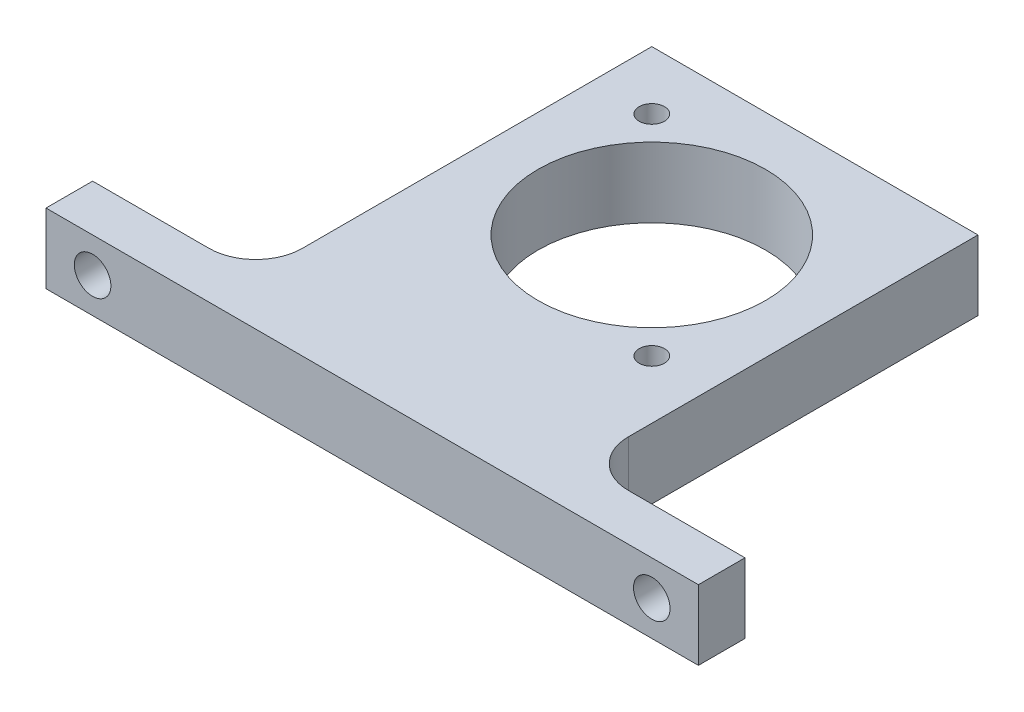
SolidWorks part; units mm, degrees
material "6061-T6 (SS)"
ref_plane "Front Plane" through (0, 0, 0) normal (0, 0, 1) x (1, 0, 0)
ref_plane "Top Plane" through (0, 0, 0) normal (0, 1, 0) x (1, 0, 0)
ref_plane "Right Plane" through (0, 0, 0) normal (1, 0, 0) x (0, 0, -1)
sketch "Sketch1" plane through (0, 0, 0) normal (0, 1, 0) x (1, 0, 0)
  line L1 (-22.225, 22.225) -> (22.225, 22.225)
  line L2 (-22.225, 22.225) -> (-22.225, -38.1)
  line L3 (-22.225, -38.1) -> (22.225, -38.1)
  line L4 (22.225, 22.225) -> (22.225, -38.1)
  circle A0 centre (0, 0) radius 11.1125 construction
  point P7 (0, 22.225)
  dimension "D1" = 22.225
  dimension "D2" = 38.1
  dimension "D3" = 22.225
  dimension "D4" = 22.225
extrude "Boss-Extrude1" add sketch "Sketch1" along normal blind 9.525
sketch "Sketch2" plane through (0, 0, 0) normal (0, -1, 0) x (1, 0, 0)
  line L0 (-22.225, -22.225) -> (-22.225, 38.1) construction
  line L1 (-22.225, 38.1) -> (22.225, 38.1) construction
  line L2 (22.225, 38.1) -> (22.225, -22.225) construction
  line L3 (22.225, -22.225) -> (-22.225, -22.225) construction
  line L4 (-22.225, -22.225) -> (-22.225, 38.1)
  line L5 (-22.225, 38.1) -> (22.225, 38.1)
  line L6 (22.225, 38.1) -> (22.225, -22.225)
  line L7 (22.225, -22.225) -> (-22.225, -22.225)
sketch "Sketch6" plane through (0, 9.525, 0) normal (0, 1, 0) x (1, 0, 0)
  line L9 (-22.225, 22.225) -> (-22.225, -38.1)
  line L10 (-22.225, -38.1) -> (22.225, -38.1)
  line L11 (22.225, -38.1) -> (22.225, 22.225)
  line L12 (22.225, 22.225) -> (-22.225, 22.225)
  line L13 (-22.225, 22.225) -> (-22.225, -38.1) construction
  line L14 (-22.225, -38.1) -> (22.225, -38.1) construction
  line L15 (22.225, -38.1) -> (22.225, 22.225) construction
  line L16 (22.225, 22.225) -> (-22.225, 22.225) construction
  dimension "D1" = 0
sketch "Sketch7" plane through (0, 0, 38.1) normal (0, 0, 1) x (1, 0, 0)
  line L0 (-22.225, 9.525) -> (-44.45, 9.525)
  line L1 (-44.45, 9.525) -> (-44.45, 0)
  line L2 (-44.45, 0) -> (44.45, 0)
  line L3 (44.45, 0) -> (44.45, 9.525)
  line L4 (-22.225, 9.525) -> (-22.225, 0)
  line L5 (-22.225, 0) -> (22.225, 0)
  line L6 (22.225, 0) -> (22.225, 9.525)
  line L7 (22.225, 9.525) -> (-22.225, 9.525)
  line L8 (-22.225, 9.525) -> (-22.225, 0) construction
  line L10 (22.225, 0) -> (22.225, 9.525) construction
  line L11 (22.225, 9.525) -> (-22.225, 9.525) construction
  line L12 (44.45, 9.525) -> (-44.45, 9.525)
  line L17 (-22.225, 0) -> (22.225, 0)
  point P8 (0, 0)
  point P9 (0, 9.525)
  dimension "D2" = 88.9
  dimension "D1" = 0
extrude "Boss-Extrude3" add sketch "Sketch7" against normal blind 6.35
fillet "Fillet1" radius 6.35 2 edges at (22.225, 4.7625, 31.75) (-22.225, 4.7625, 31.75)
sketch "Sketch8" plane through (0, 0, 38.1) normal (0, 0, 1) x (1, 0, 0)
  line L1 (44.45, 0) -> (44.45, 9.525) construction
  line L2 (0, 0) -> (0, 30.8683) construction
  circle A0 centre (-38.1, 4.7625) radius 2.4892
  circle A1 centre (38.1, 4.7625) radius 2.4892
  point P9 (44.45, 4.7625)
  dimension "D1" = 4.9784
  dimension "D2" = 38.1
extrude "Cut-Extrude1" cut sketch "Sketch8" against normal up to surface (6.35 mm away)
sketch "Sketch9" plane through (0, 0, 38.1) normal (0, 0, 1) x (1, 0, 0)
  line L0 (0, 0) -> (0, 29.1158) construction
  circle A2 centre (-38.1, 1.9844) radius 3.4925
  circle A3 centre (38.1, 1.9844) radius 3.4925
  dimension "D1" = 6.985
  dimension "D2" = 38.1
sketch "Sketch10" plane through (0, 9.525, 0) normal (0, 1, 0) x (1, 0, 0)
  line L0 (29.8509, -29.8509) -> (-29.8509, 29.8509) construction
  line L1 (0, 0) -> (0, 68.8246) construction
  circle A0 centre (0, 0) radius 15.494
  circle A1 centre (0, 0) radius 20.193 construction
  circle A2 centre (-14.2786, 14.2786) radius 1.7272
  circle A3 centre (14.2786, -14.2786) radius 1.7272
  point P6 (0, 0)
  dimension "D1" = 30.988
  dimension "D2" = 3.4544
  dimension "D3" = 40.386
  dimension "D4" = 45
extrude "Cut-Extrude2" cut sketch "Sketch10" against normal up to next
hole_wizard "#8-32 Tapped Hole2" positions "Sketch13" profile "Sketch14" tap size "#8-32" standard "ANSI Inch" end condition through all
sketch "Sketch13" plane through (0, 9.525, 0) normal (0, 1, 0) x (1, 0, 0)
  point P0 (-14.2786, 14.2786)
  point P3 (14.2786, -14.2786)
sketch "Sketch14" plane through (-14.2786, 9.525, -14.2786) normal (1, 0, 0) x (0, 0, 1)
  line L0 (0, 0) -> (0, 9.525)
  line L1 (0, 9.525) -> (1.7272, 9.525)
  line L2 (1.7272, 9.525) -> (1.7272, 0)
  line L5 (1.7272, 0) -> (0, 0)
  line L11 (0, -6.35) -> (0, 107.95) construction
  dimension "Thru Tap Drill Dia." = 3.4544
  dimension "Thru Tap Drill Depth" = 9.525
